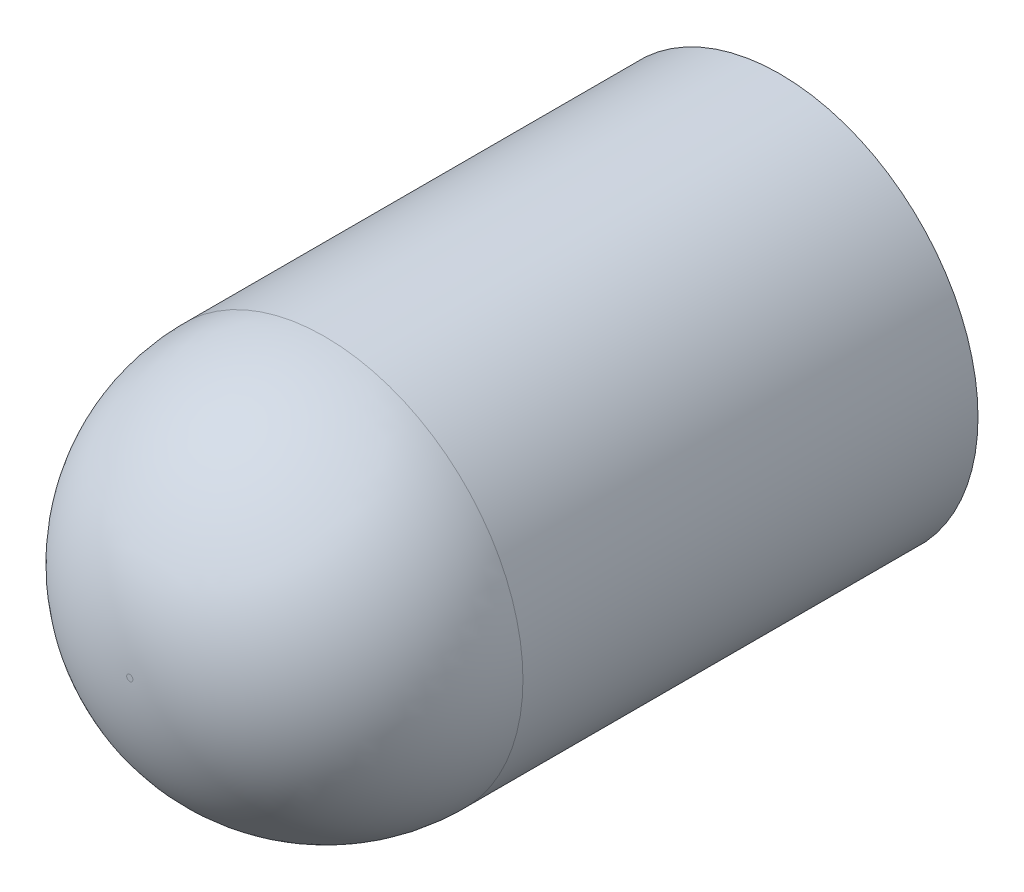
SolidWorks part; units mm, degrees
ref_plane "Front" through (0, 0, 0) normal (0, 0, 1) x (1, 0, 0)
ref_plane "Top" through (0, 0, 0) normal (0, 1, 0) x (1, 0, 0)
ref_plane "Right" through (0, 0, 0) normal (1, 0, 0) x (0, 0, -1)
sketch "Sketch1" plane through (0, 0, 0) normal (0, 0, 1) x (1, 0, 0)
  circle A0 centre (0, 0) radius 3.048
  dimension "D1" = 6.096
extrude "Boss-Extrude1" add sketch "Sketch1" along normal blind 10
fillet "Fillet2" radius 3 1 edges at (3.048, 0, 10)
